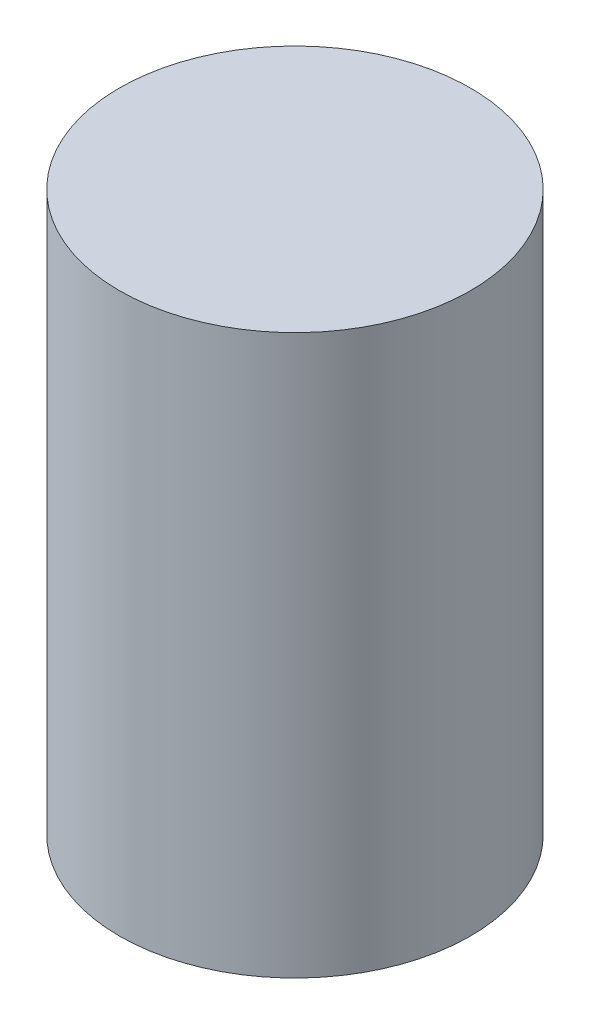
SolidWorks part; units mm, degrees
ref_plane "Front Plane" through (0, 0, 0) normal (0, 0, 1) x (1, 0, 0)
ref_plane "Top Plane" through (0, 0, 0) normal (0, 1, 0) x (1, 0, 0)
ref_plane "Right Plane" through (0, 0, 0) normal (1, 0, 0) x (0, 0, -1)
sketch "Sketch1" plane through (0, 0, 0) normal (0, 1, 0) x (1, 0, 0)
  circle A0 centre (0, 0) radius 797.687
  dimension "D1" = 1595.374
extrude "Extrude1" add sketch "Sketch1" along normal mid plane 2540
